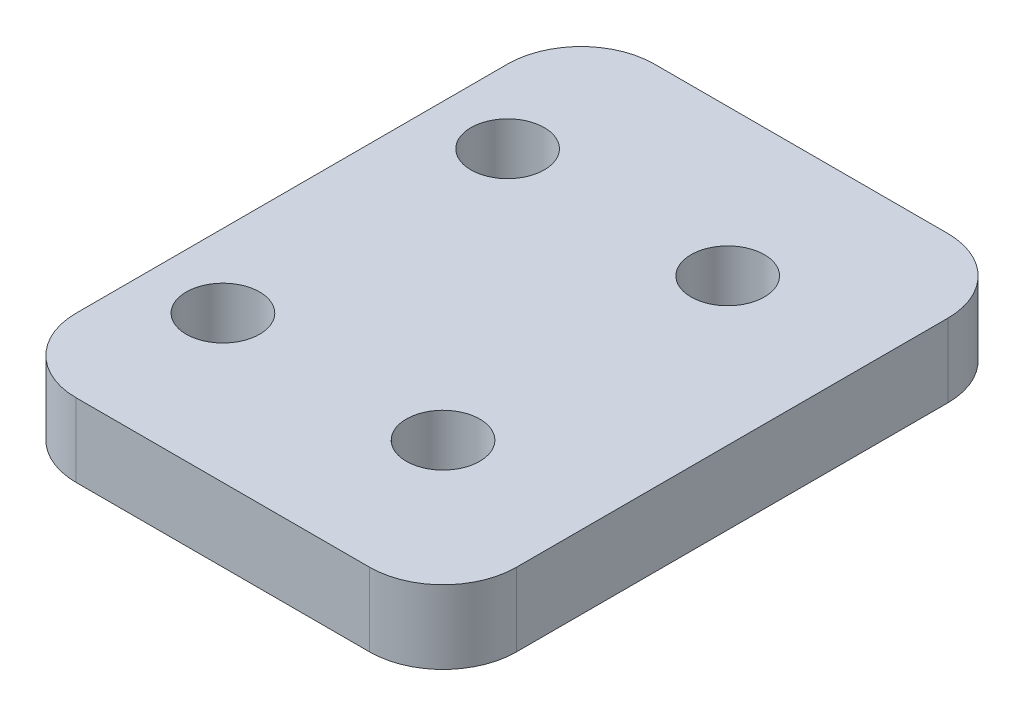
SolidWorks part; units mm, degrees
ref_plane "Front" through (0, 0, 0) normal (0, 0, 1) x (1, 0, 0)
ref_plane "Top" through (0, 0, 0) normal (0, 1, 0) x (1, 0, 0)
ref_plane "Right" through (0, 0, 0) normal (1, 0, 0) x (0, 0, -1)
sketch "Sketch1" plane through (0, 0, 0) normal (0, 1, 0) x (1, 0, 0)
  line L0 (-19.05, -12.319) -> (19.05, -12.319) construction
  line L1 (-19.05, -25.019) -> (19.05, -25.019)
  line L2 (-19.05, -25.019) -> (-19.05, 25.019)
  line L3 (-19.05, 25.019) -> (19.05, 25.019)
  line L4 (19.05, -25.019) -> (19.05, 25.019)
  line L5 (-19.05, -25.019) -> (19.05, 25.019) construction
  line L6 (-19.05, 25.019) -> (19.05, -25.019) construction
  circle A0 centre (6.35, -12.319) radius 3.175
  circle A1 centre (-12.7, -12.319) radius 3.175
  circle A2 centre (-12.7, 12.319) radius 3.175
  circle A3 centre (6.35, 12.319) radius 3.175
  point P0 (0, 0)
  dimension "D2" = 6.35
  dimension "D1" = 19.05
  dimension "D3" = 12.7
  dimension "D5" = 12.7
  dimension "D7" = 24.638
  dimension "D8" = 12.7
  dimension "D4" = 6.35
  dimension "D6" = 2
extrude "Boss-Extrude1" add sketch "Sketch1" along normal blind 6.35
fillet "Fillet1" radius 6.35 4 edges at (19.05, 3.175, 25.019) (-19.05, 3.175, 25.019) (19.05, 3.175, -25.019) (-19.05, 3.175, -25.019)
equation "\"D5@Sketch1\"=\"D3@Sketch1\""
equation "\"D8@Sketch1\"=\"D3@Sketch1\""
